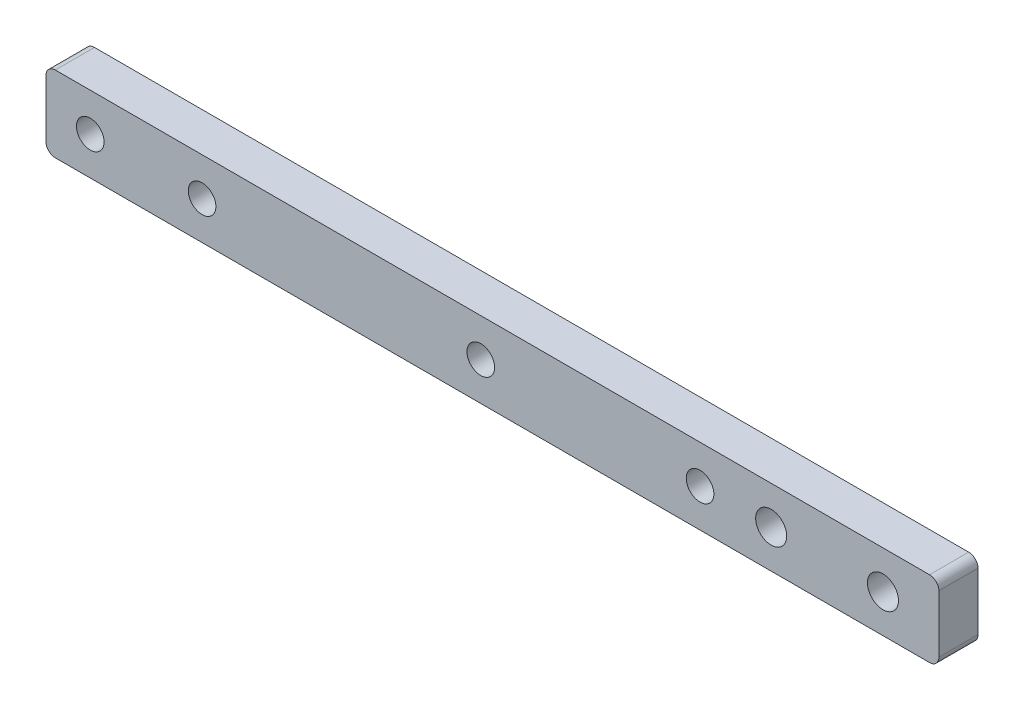
SolidWorks part; units mm, degrees
ref_plane "Front" through (0, 0, 0) normal (0, 0, 1) x (1, 0, 0)
ref_plane "Top" through (0, 0, 0) normal (0, 1, 0) x (1, 0, 0)
ref_plane "Right" through (0, 0, 0) normal (1, 0, 0) x (0, 0, -1)
sketch "Sketch1" plane through (0, 0, 0) normal (0, 0, 1) x (1, 0, 0)
  line L0 (59.309, 3.1115) -> (68.453, 3.1115) construction
  line L1 (0, 6.223) -> (73.025, 6.223)
  line L2 (0, 6.223) -> (0, 0)
  line L3 (0, 0) -> (73.025, 0)
  line L4 (73.025, 6.223) -> (73.025, 0)
  line L5 (63.881, 6.223) -> (63.881, 0) construction
  line L6 (3.6195, 3.1115) -> (12.7635, 3.1115) construction
  line L8 (8.1915, 6.223) -> (8.1915, 0) construction
  circle A0 centre (59.309, 3.1115) radius 1.27
  circle A1 centre (68.453, 3.1115) radius 1.27
  circle A2 centre (3.6195, 3.1115) radius 1.1303
  circle A3 centre (12.7635, 3.1115) radius 1.1303
  point P9 (63.881, 3.1115)
  point P20 (8.1915, 3.1115)
  dimension "D5" = 2.54
  dimension "D6" = 2.2606
  dimension "D1" = 73.025
  dimension "D2" = 6.223
  dimension "D3" = 9.144
  dimension "D4" = 9.144
  dimension "D7" = 8.1915
extrude "Boss-Extrude1" add sketch "Sketch1" along normal blind 3.2004
sketch "Sketch2" plane through (0, 0, 3.2004) normal (0, 0, 1) x (1, 0, 0)
  line L0 (0, 3.1115) -> (35.56, 3.1115) construction
  line L1 (0, 6.223) -> (0, 0) construction
  line L2 (53.4924, 3.1115) -> (73.025, 3.1115) construction
  line L3 (73.025, 0) -> (73.025, 6.223) construction
  circle A0 centre (35.56, 3.1115) radius 1.1303
  circle A1 centre (53.4924, 3.1115) radius 1.1303
  dimension "D2" = 2.2606
  dimension "D1" = 35.56
  dimension "D3" = 19.5326
extrude "Cut-Extrude1" cut sketch "Sketch2" against normal up to surface (3.2004 mm away) up to face at (36.5125, 3.1115, 0)
fillet "Fillet1" radius 0.762 4 edges at (0, 0, 1.6002) (73.025, 0, 1.6002) (73.025, 6.223, 1.6002) (0, 6.223, 1.6002)
